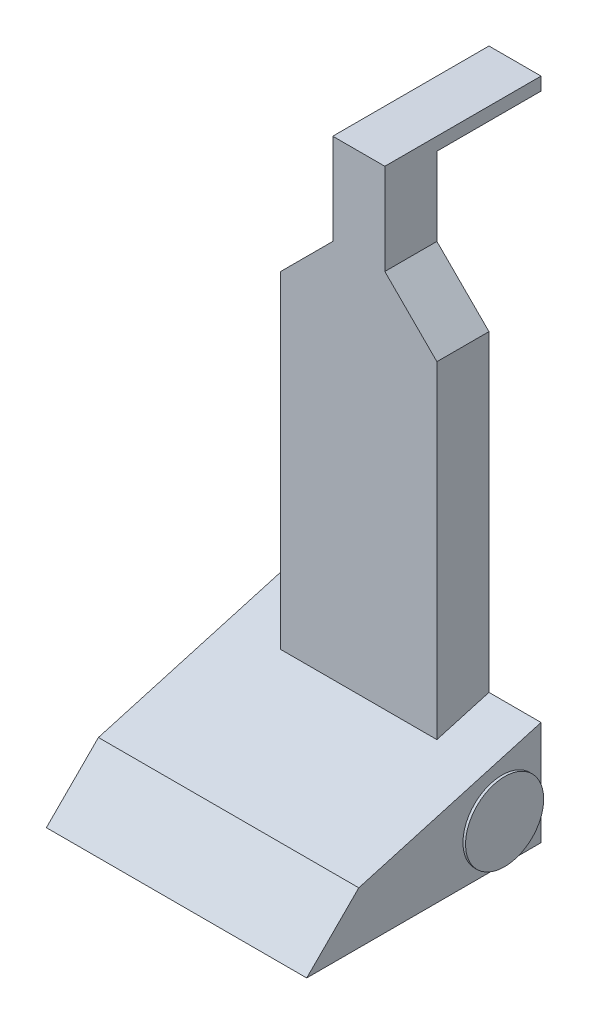
SolidWorks part; units mm, degrees
ref_plane "Front" through (0, 0, 0) normal (0, 0, 1) x (1, 0, 0)
ref_plane "Top" through (0, 0, 0) normal (0, 1, 0) x (1, 0, 0)
ref_plane "Right" through (0, 0, 0) normal (1, 0, 0) x (0, 0, -1)
sketch "Sketch1" plane through (0, 0, 0) normal (1, 0, 0) x (0, 0, -1)
  line L0 (0, 40) -> (0, 0)
  line L1 (0, 0) -> (-90, 0)
  line L2 (-90, 0) -> (-70, 20)
  line L3 (-70, 20) -> (0, 40)
  dimension "D1" = 40
  dimension "D2" = 90
extrude "Extrude1" add sketch "Sketch1" along normal mid plane 100
sketch "Sketch2" plane through (50, 0, 0) normal (1, 0, 0) x (0, 0, -1)
  circle A0 centre (-15, 15) radius 15
extrude "Extrude2" add sketch "Sketch2" along normal blind 1 separate body
sketch "Sketch3" plane through (-50, 0, 0) normal (-1, 0, 0) x (0, 0, 1)
  circle A0 centre (15, 15) radius 15
extrude "Extrude3" add sketch "Sketch3" along normal blind 1 separate body
sketch "Sketch4" plane through (0, 0, 0) normal (0, 1, 0) x (1, 0, 0)
  line L0 (-30, 0) -> (30, 0)
  line L2 (-30, 0) -> (-30, -20)
  line L3 (30, 0) -> (30, -20)
  line L4 (-30, -20) -> (30, -20)
  line L5 (-50, 0) -> (50, 0) construction
  line L6 (-50, -20) -> (50, -20) construction
extrude "Extrude4" add sketch "Sketch4" along normal blind 180
chamfer "Chamfer1" distance 20 2 edges at (-30, 180, 10) (30, 180, 10)
sketch "Sketch5" plane through (0, 180, 0) normal (0, 1, 0) x (-1, 0, 0)
  line L1 (-10, 20) -> (10, 20)
  line L2 (-10, 20) -> (-10, 0)
  line L3 (-10, 0) -> (10, 0)
  line L4 (10, 20) -> (10, 0)
extrude "Extrude5" add sketch "Sketch5" along normal blind 30
sketch "Sketch6" plane through (0, 210, 0) normal (0, 1, 0) x (-1, 0, 0)
  line L1 (-10, 20) -> (10, 20)
  line L2 (-10, 20) -> (-10, -40)
  line L3 (-10, -40) -> (10, -40)
  line L4 (10, 20) -> (10, -40)
  dimension "D1" = 60
  dimension "D2" = 20
extrude "Extrude6" add sketch "Sketch6" along normal blind 5
